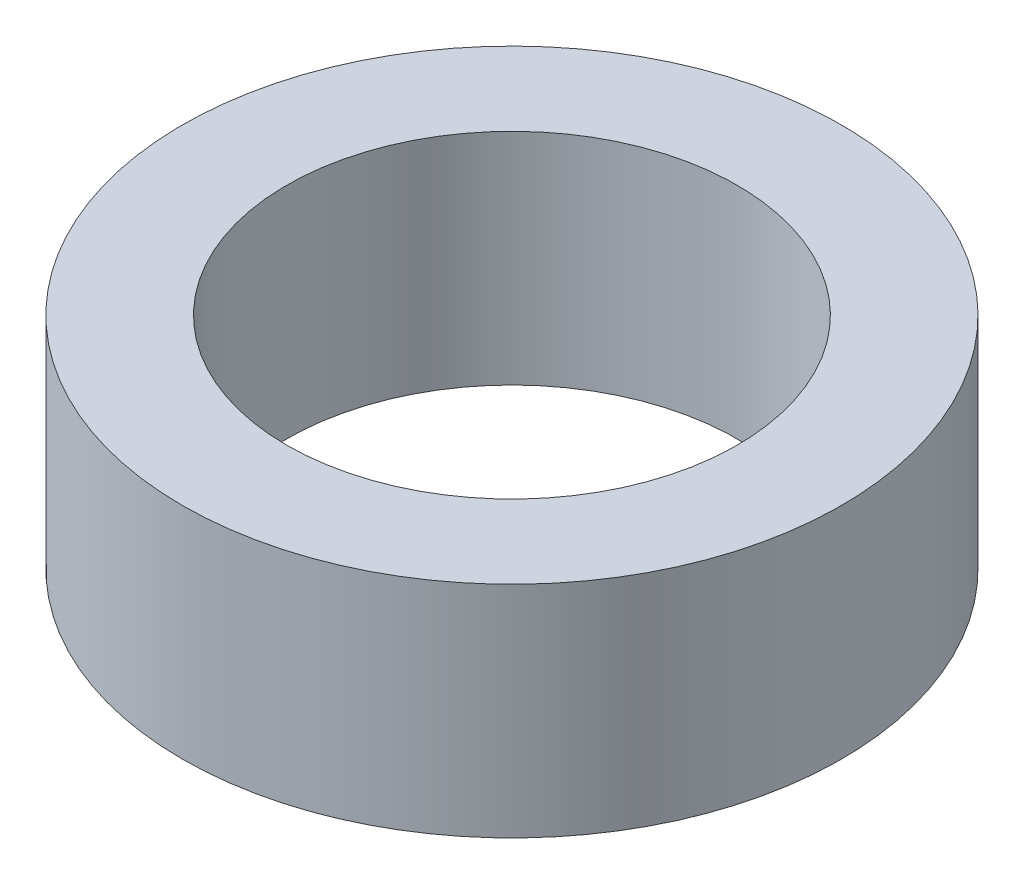
SolidWorks part; units mm, degrees
material "6061 合金"
ref_plane "前视基准面" through (0, 0, 0) normal (0, 0, 1) x (1, 0, 0)
ref_plane "上视基准面" through (0, 0, 0) normal (0, 1, 0) x (1, 0, 0)
ref_plane "右视基准面" through (0, 0, 0) normal (1, 0, 0) x (0, 0, -1)
sketch "草图1" plane through (0, 0, 0) normal (0, 1, 0) x (1, 0, 0)
  circle A0 centre (0, 0) radius 2.05
  circle A1 centre (0, 0) radius 3
  dimension "D1" = 6
  dimension "D2" = 4.1
extrude "凸台-拉伸1" add sketch "草图1" along normal blind 2
